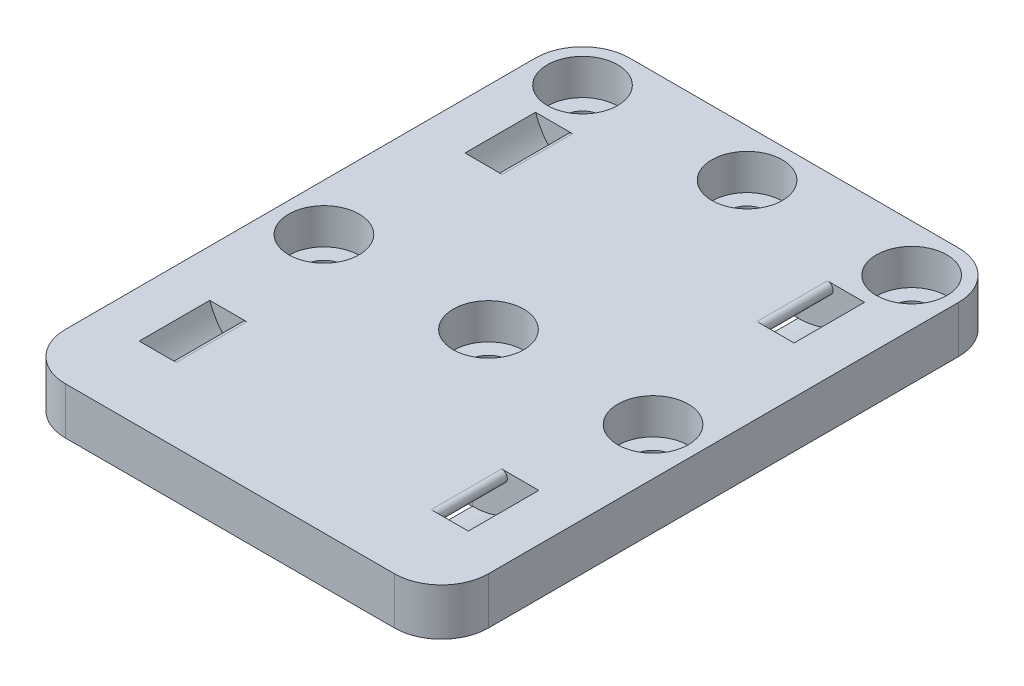
SolidWorks part; units mm, degrees
material "PET"
ref_plane "Front" through (0, 0, 0) normal (0, 0, 1) x (1, 0, 0)
ref_plane "Top" through (0, 0, 0) normal (0, 1, 0) x (1, 0, 0)
ref_plane "Right" through (0, 0, 0) normal (1, 0, 0) x (0, 0, -1)
sketch "Sketch1" plane through (0, 0, 0) normal (0, 1, 0) x (1, 0, 0)
  line L1 (22.225, -38.1) -> (-22.225, -38.1)
  line L2 (28.575, -31.75) -> (28.575, 31.75)
  line L3 (22.225, 38.1) -> (-22.225, 38.1)
  line L4 (-28.575, -31.75) -> (-28.575, 31.75)
  line L5 (28.575, -38.1) -> (-28.575, 38.1) construction
  line L6 (28.575, 38.1) -> (-28.575, -38.1) construction
  arc A0 (-22.225, -38.1) -> (-28.575, -31.75) centre (-22.225, -31.75) cw
  arc A1 (22.225, -38.1) -> (28.575, -31.75) centre (22.225, -31.75) ccw
  arc A2 (28.575, 31.75) -> (22.225, 38.1) centre (22.225, 31.75) ccw
  arc A3 (-22.225, 38.1) -> (-28.575, 31.75) centre (-22.225, 31.75) ccw
  point P0 (0, 0)
  dimension "D3" = 6.35
  dimension "D1" = 57.15
  dimension "D2" = 76.2
extrude "Boss-Extrude1" add sketch "Sketch1" along normal blind 6.35
sketch "Sketch4" plane through (0, 6.35, 0) normal (0, 1, 0) x (1, 0, 0)
  arc A0 (28.575, 31.75) -> (22.225, 38.1) centre (22.225, 31.75) ccw construction
  point P0 (-22.225, 31.75)
  point P8 (0, 31.75)
  point P9 (22.225, 31.75)
  point P10 (0, -3.175)
  point P11 (22.225, -3.175)
  point P12 (-22.225, -3.175)
  point P13 (0, 0)
  point P17 (0, 0)
  dimension "D3" = 34.925
  dimension "D2" = 3
  dimension "D1" = 2
hole_wizard "CBORE for #10 Socket Head Cap Screw1" positions "Sketch4" profile "Sketch3" counterbore size "#10" standard "ANSI Inch" end condition through all
sketch "Sketch3" plane through (-22.225, 6.35, -31.75) normal (1, 0, 0) x (0, 0, 1)
  line L0 (0, 0) -> (0, 6.35)
  line L1 (0, 6.35) -> (2.5527, 6.35)
  line L3 (2.5527, 6.35) -> (2.5527, 4.826)
  line L4 (2.5527, 4.826) -> (4.7625, 4.826)
  line L5 (4.7625, 4.826) -> (4.7625, 0)
  line L7 (4.7625, 0) -> (0, 0)
  line L11 (0, -6.35) -> (0, 107.95) construction
  dimension "Thru Hole Dia." = 5.1054
  dimension "Thru Hole Depth" = 6.35
  dimension "C'Bore Dia." = 9.525
  dimension "C'Bore Depth" = 4.826
sketch "Sketch5" plane through (0, 0, 0) normal (1, 0, 0) x (0, 0, -1)
  line L0 (-31.75, 0) -> (31.75, 0) construction
  line L1 (25.4, 0) -> (15.875, 0)
  line L2 (25.4, 0) -> (25.4, 3.175)
  line L3 (25.4, 3.175) -> (15.875, 3.175)
  line L4 (15.875, 0) -> (15.875, 3.175)
  line L5 (38.1, 6.35) -> (38.1, 0) construction
  line L6 (-18.6, 0) -> (-28.125, 0)
  line L7 (-18.6, 0) -> (-18.6, 3.175)
  line L8 (-18.6, 3.175) -> (-28.125, 3.175)
  line L9 (-28.125, 0) -> (-28.125, 3.175)
  point P10 (22.8489, 3.175)
  dimension "D1" = 9.525
  dimension "D2" = 3.175
  dimension "D3" = 44
  dimension "D4" = 12.7
sketch "Sketch6" plane through (0, 0, 0) normal (0, 0, 1) x (1, 0, 0)
  line L0 (-13.2447, 0) -> (13.2447, 0)
  line L1 (-22.225, 0) -> (22.225, 0) construction
  line L2 (-22.225, 6.35) -> (22.225, 6.35) construction
  arc A0 (13.2447, 0) -> (22.225, 6.35) centre (13.2447, 9.525) ccw
  arc A1 (-13.2447, 0) -> (-22.225, 6.35) centre (-13.2447, 9.525) cw
  point P8 (0, 0)
  point P11 (0, 0)
  point P14 (0, 0)
  dimension "D2" = 9.525
  dimension "D1" = 44.45
sweep "Cut-Sweep1" cut profiles "Sketch5" path "Sketch6"
fillet "Fillet1" radius 0.762 4 edges at (-18.744, 6.35, 23.3625) (18.744, 6.35, 23.3625) (-18.744, 6.35, -20.6375) (18.744, 6.35, -20.6375)
